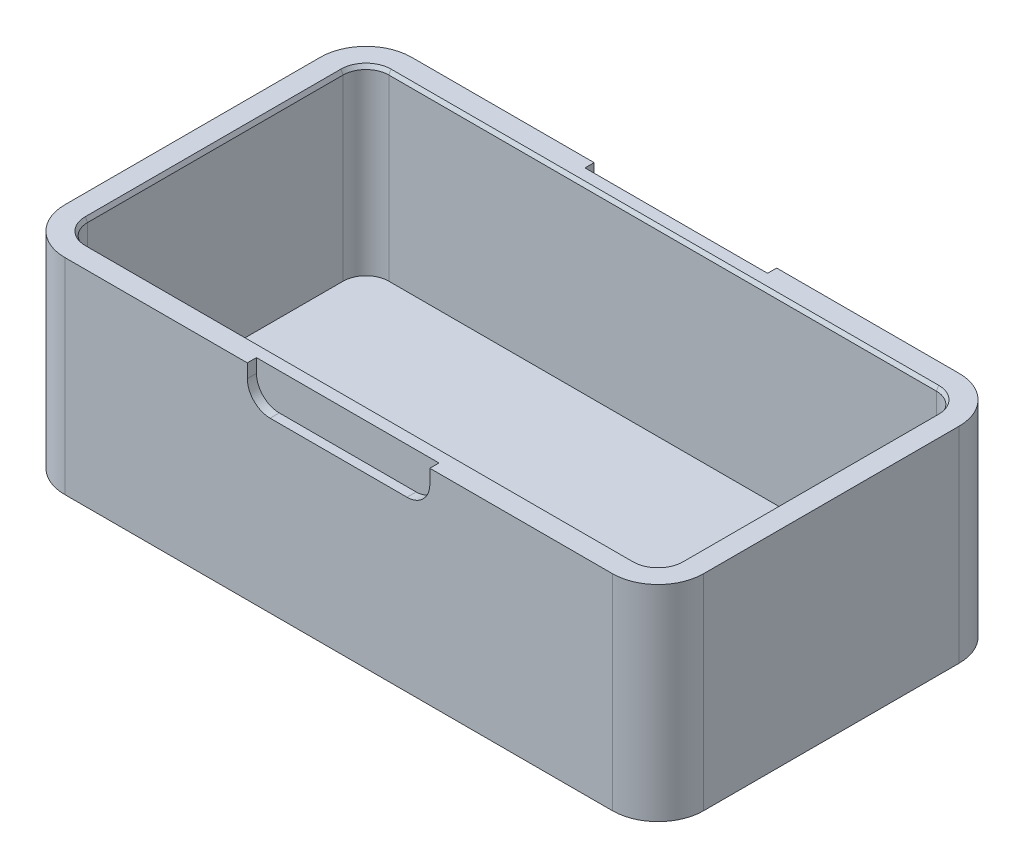
SolidWorks part; units mm, degrees
ref_plane "Front" through (0, 0, 0) normal (0, 0, 1) x (1, 0, 0)
ref_plane "Top" through (0, 0, 0) normal (0, 1, 0) x (1, 0, 0)
ref_plane "Right" through (0, 0, 0) normal (1, 0, 0) x (0, 0, -1)
sketch "Sketch1" plane through (0, 0, 0) normal (0, 1, 0) x (1, 0, 0)
  line L1 (0, 0) -> (140, 0)
  line L2 (0, 0) -> (0, 76)
  line L3 (0, 76) -> (140, 76)
  line L4 (140, 0) -> (140, 76)
  dimension "D1" = 140
  dimension "D2" = 76
extrude "Boss-Extrude1" add sketch "Sketch1" along normal blind 45
fillet "Fillet2" radius 10 4 edges at (140, 22.5, -76) (140, 22.5, 0) (0, 22.5, -76) (0, 22.5, 0)
sketch "Sketch4" plane through (0, 45, 0) normal (0, 1, 0) x (1, 0, 0)
  line L8 (135, 10) -> (135, 66)
  line L9 (130, 71) -> (10, 71)
  line L10 (5, 66) -> (5, 10)
  line L11 (10, 5) -> (130, 5)
  line L12 (135, 10) -> (135, 66)
  line L13 (130, 71) -> (10, 71)
  line L14 (5, 66) -> (5, 10)
  line L15 (10, 5) -> (130, 5)
  arc A8 (135, 66) -> (130, 71) centre (130, 66) ccw
  arc A9 (10, 71) -> (5, 66) centre (10, 66) ccw
  arc A10 (5, 10) -> (10, 5) centre (10, 10) ccw
  arc A11 (130, 5) -> (135, 10) centre (130, 10) ccw
  arc A12 (135, 66) -> (130, 71) centre (130, 66) ccw
  arc A13 (10, 71) -> (5, 66) centre (10, 66) ccw
  arc A14 (5, 10) -> (10, 5) centre (10, 10) ccw
  arc A15 (130, 5) -> (135, 10) centre (130, 10) ccw
  dimension "D1" = 5
extrude "Cut-Extrude2" cut sketch "Sketch4" against normal blind 40
sketch "Sketch5" plane through (0, 0, 0) normal (0, 0, 1) x (1, 0, 0)
  line L0 (10, 45) -> (130, 45) construction
  line L1 (50, 45) -> (90, 45)
  line L2 (50, 45) -> (50, 37)
  line L3 (50, 37) -> (90, 37)
  line L4 (90, 45) -> (90, 37)
  line L5 (70, 0) -> (70, 45) construction
  line L6 (10, 0) -> (130, 0) construction
  dimension "D1" = 40
  dimension "D2" = 8
extrude "Cut-Extrude3" cut sketch "Sketch5" against normal blind 2
fillet "Fillet3" radius 5 2 edges at (90, 37, -1) (50, 37, -1)
ref_plane "Plane1" through (0, 0, -38) normal (0, 0, 1) x (1, 0, 0)
mirror "Mirror1" about plane through (0, 0, -38) normal (0, 0, 1) of "Fillet3", "Cut-Extrude3"
chamfer "Chamfer1" distance 0.5 angle 60 8 edges at (70, 45, -5) (133.5355, 45, -6.4645) (6.4645, 45, -6.4645) (135, 45, -38) (5, 45, -38) (133.5355, 45, -69.5355) (6.4645, 45, -69.5355) (70, 45, -71)
